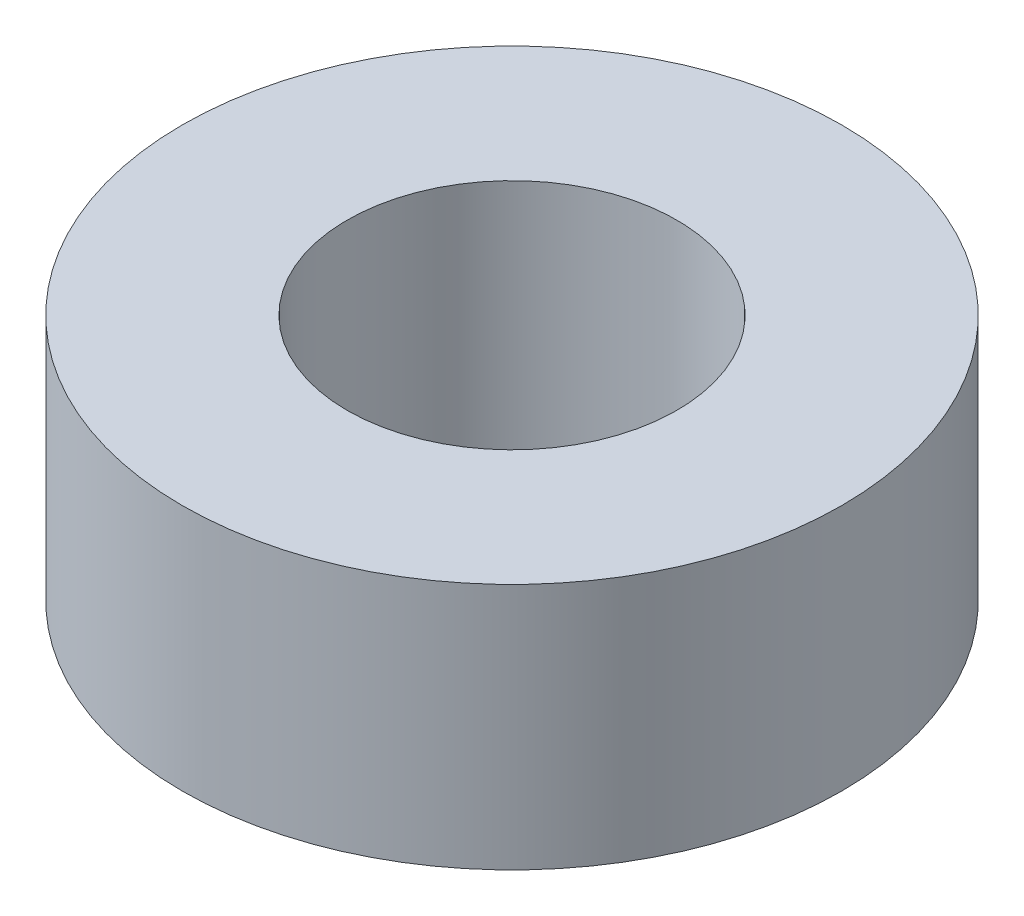
SolidWorks part; units mm, degrees
ref_plane "Front Plane" through (0, 0, 0) normal (0, 0, 1) x (1, 0, 0)
ref_plane "Top Plane" through (0, 0, 0) normal (0, 1, 0) x (1, 0, 0)
ref_plane "Right Plane" through (0, 0, 0) normal (1, 0, 0) x (0, 0, -1)
sketch "Sketch2" plane through (0, 0, 0) normal (0, 1, 0) x (1, 0, 0)
  circle A0 centre (0, 0) radius 4
extrude "Boss-Extrude1" add sketch "Sketch2" along normal blind 3
sketch "Sketch3" plane through (0, 0, 0) normal (0, 1, 0) x (1, 0, 0)
  circle A0 centre (0, 0) radius 2
extrude "Cut-Extrude1" cut sketch "Sketch3" along normal blind 3
